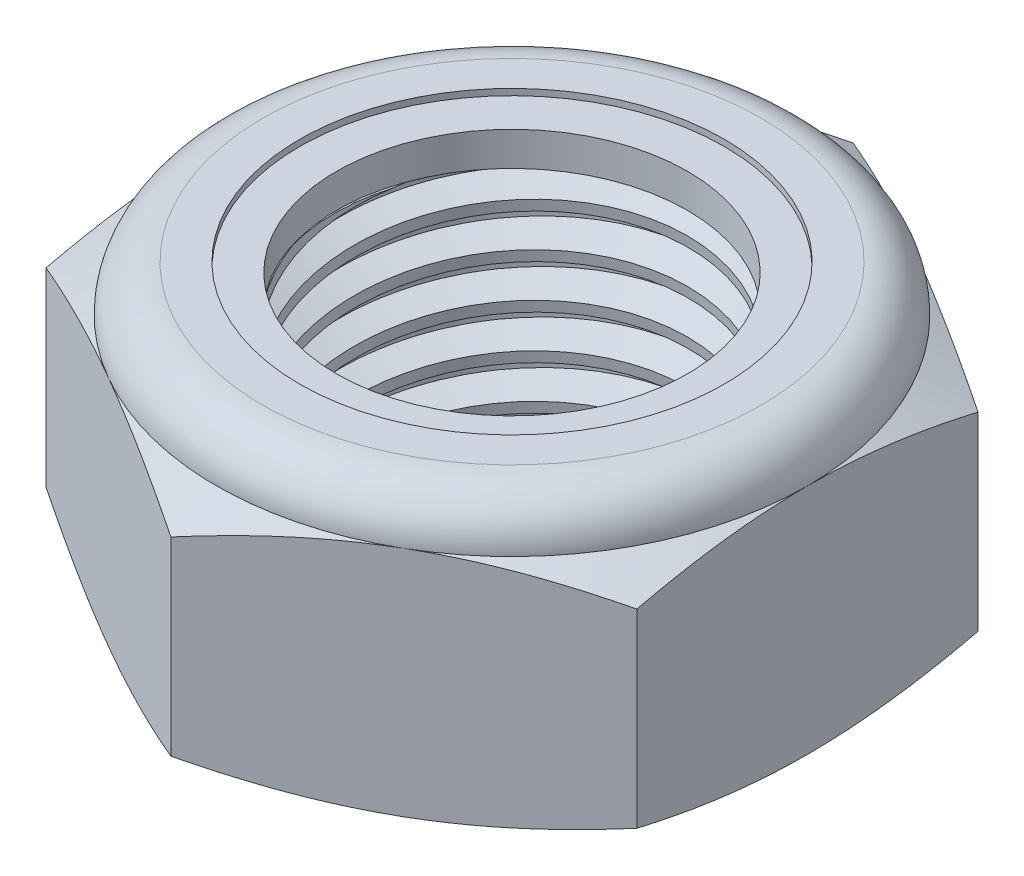
SolidWorks part; units mm, degrees
ref_plane "Front" through (0, 0, 0) normal (0, 0, 1) x (1, 0, 0)
ref_plane "Top" through (0, 0, 0) normal (0, 1, 0) x (1, 0, 0)
ref_plane "Right" through (0, 0, 0) normal (1, 0, 0) x (0, 0, -1)
sketch "Sketch1" plane through (0, 0, 0) normal (0, 1, 0) x (1, 0, 0)
  line L1 (0, 8.2489) -> (-7.1438, 4.1244)
  line L2 (-7.1438, 4.1244) -> (-7.1438, -4.1244)
  line L3 (-7.1438, -4.1244) -> (0, -8.2489)
  line L4 (0, -8.2489) -> (7.1437, -4.1244)
  line L5 (7.1437, -4.1244) -> (7.1437, 4.1244)
  line L6 (7.1437, 4.1244) -> (0, 8.2489)
  circle A0 centre (0, 0) radius 7.1438 construction
  dimension "Hex Flats" = 14.2875
extrude "Extrude1" add sketch "Sketch1" along normal blind 6.7469
sketch "Sketch2" plane through (0, 0, 0) normal (1, 0, 0) x (0, 0, -1)
  line L0 (-4.7625, 0) -> (-4.7625, 6.7469) construction
  line L1 (0, 0) -> (4.7625, 0)
  line L2 (0, 0) -> (0, 6.7469)
  line L3 (0, 6.7469) -> (4.7625, 6.7469)
  line L4 (4.7625, 0) -> (4.7625, 6.7469)
  line L5 (-4.1244, 6.7469) -> (4.1244, 6.7469) construction
  line L7 (0, -4.7625) -> (0, 0) construction
  dimension "Thread Dia" = 9.525
revolve "Revolve1" add sketch "Sketch2" angle 360 about L7
sketch "Sketch3" plane through (0, 0, 0) normal (1, 0, 0) x (0, 0, -1)
  line L0 (4.7625, 6.7469) -> (-4.7625, 6.7469) construction
  line L1 (-4.7625, 6.7469) -> (-4.7625, 5.6885) construction
  line L2 (-4.7625, 5.6885) -> (4.7625, 6.7469) construction
  line L3 (4.7625, 6.7469) -> (4.7771, 6.6154) construction
  line L4 (4.7771, 6.6154) -> (4.8794, 5.695)
  line L5 (4.8794, 5.695) -> (4.2735, 5.9605)
  line L6 (4.2735, 5.9605) -> (4.2443, 6.2234)
  line L7 (4.2443, 6.2234) -> (4.7771, 6.6154)
  line L8 (4.2589, 6.0919) -> (4.8282, 6.1552) construction
  line L9 (4.7625, 6.7469) -> (4.7625, 6.1479) construction
  line L10 (4.7625, 6.1479) -> (-4.7625, 5.0896) construction
  line L11 (-4.7625, 5.0896) -> (-4.7625, 5.6885) construction
  line L12 (-0.1253, 6.7469) -> (0.1253, 4.4906) construction
  line L13 (-4.7625, 0) -> (-4.7625, 6.7469) construction
  line L14 (0, 6.7469) -> (4.7625, 6.7469) construction
  line L15 (4.7625, 0) -> (4.7625, 6.7469) construction
  point P13 (0, 5.6187)
  dimension "D1" = 0.1323
  dimension "D2" = 0.2646
  dimension "Thread Pitch" = 1.0583
  dimension "D4" = 60
  dimension "D5" = 1.0583
revolve "Cut-Revolve1" cut sketch "Sketch3" angle 360 about L12
pattern_linear "LPattern1" count 6 spacing 1.0583 along (0, -1, 0) count 2 spacing 1.0583 along (0, 1, 0) of "Cut-Revolve1"
sketch "Sketch4" plane through (0, 0, 0) normal (1, 0, 0) x (0, 0, -1)
  line L0 (0, 6.7469) -> (4.7625, 6.7469)
  line L1 (4.7625, 6.7469) -> (4.2443, 6.5052)
  line L2 (4.2443, 6.5052) -> (4.2443, 0.2416)
  line L3 (4.2443, 0.2416) -> (4.7625, 0)
  line L4 (4.7625, 0) -> (0, 0)
  line L5 (0, 0) -> (0, 6.7469)
  line L6 (4.7625, 0) -> (4.7625, 6.7469) construction
  line L7 (0, 6.7469) -> (4.7625, 6.7469) construction
  line L8 (0, 0) -> (4.7625, 0) construction
  line L9 (0, 0) -> (0, 6.7469) construction
  line L10 (0, 6.7469) -> (0, 7.3186) construction
  dimension "D1" = 25
revolve "Cut-Revolve2" cut sketch "Sketch4" angle 360 about L10
combine bodies "Combine1" operation type subtract main body 112 bodies to subtract 111
sketch "Sketch5" plane through (0, 0, 0) normal (1, 0, 0) x (0, 0, -1)
  line L0 (0, 0) -> (7.1438, 0)
  line L1 (7.1438, 0) -> (8.2489, 0.5153)
  line L2 (8.2489, 0.5153) -> (8.2489, 5.1071)
  line L3 (8.2489, 5.1071) -> (7.1438, 5.6224)
  line L4 (6.0193, 6.7469) -> (6.0193, 8.0169)
  line L5 (6.0193, 8.0169) -> (9.5189, 8.0169)
  line L6 (9.5189, 8.0169) -> (9.5189, -1.27)
  line L7 (9.5189, -1.27) -> (0, -1.27)
  line L8 (0, -1.27) -> (0, 0)
  line L9 (7.1438, 5.6224) -> (7.1438, 0) construction
  line L10 (0, 0) -> (4.7625, 0) construction
  line L13 (8.2489, 2.8112) -> (9.5189, 2.8112) construction
  line L14 (8.2489, 6.7469) -> (8.2489, 0) construction
  line L15 (0, 0) -> (0, 8.0169) construction
  line L20 (0, 8.0169) -> (6.0193, 8.0169) construction
  line L22 (0, 6.7469) -> (4.7625, 6.7469) construction
  arc A0 (7.1438, 5.6224) -> (6.0193, 6.7469) centre (6.0193, 5.6224) ccw
  dimension "D1" = 25
  dimension "D2" = 1.27
  dimension "D3" = 6.7469
  dimension "D4" = 1.1245
revolve "Cut-Revolve3" cut sketch "Sketch5" angle 360 about L15
sketch "Sketch6" plane through (0, 0, 0) normal (1, 0, 0) x (0, 0, -1)
  line L0 (0, 5.6224) -> (6.9914, 5.6224)
  line L1 (6.0193, 6.5945) -> (5.1318, 6.5945)
  line L2 (0, 8.0169) -> (0, 5.6224)
  line L3 (5.1318, 8.0169) -> (0, 8.0169)
  line L4 (0, 8.0169) -> (6.0193, 8.0169) construction
  line L5 (0, 0) -> (0, 8.0169) construction
  line L6 (0, 8.0169) -> (0, 44.323) construction
  line L7 (5.1318, 6.5945) -> (5.1318, 8.0169)
  line L8 (6.0193, 6.7469) -> (6.0193, 6.5945) construction
  line L9 (5.1318, 6.5945) -> (4.2443, 6.5945) construction
  line L10 (4.2443, 6.5945) -> (4.2443, 6.5052) construction
  arc A0 (6.9914, 5.6224) -> (6.0193, 6.5945) centre (6.0193, 5.6224) ccw
  arc A1 (7.1438, 5.6224) -> (6.0193, 6.7469) centre (6.0193, 5.6224) ccw construction
  dimension "D1" = 0.1524
revolve "Cut-Revolve4" cut sketch "Sketch6" angle 360 about L6
sketch "Sketch7" plane through (0, 0, 0) normal (1, 0, 0) x (0, 0, -1)
  line L0 (4.2443, 5.6986) -> (6.9119, 5.6986)
  line L1 (6.0193, 6.5183) -> (4.2443, 6.5183)
  line L2 (4.2443, 6.5183) -> (4.2443, 5.6986)
  line L3 (4.2443, 5.6986) -> (0, 5.6986) construction
  line L4 (0, 5.6986) -> (0, 6.5183) construction
  line L5 (0, 6.5183) -> (4.2443, 6.5183) construction
  line L6 (4.2443, 5.6986) -> (4.2443, 5.6224) construction
  line L7 (0, 5.6224) -> (6.9914, 5.6224) construction
  line L8 (6.0193, 6.5183) -> (6.0193, 6.5945) construction
  arc A0 (6.9119, 5.6986) -> (6.0193, 6.5183) centre (6.0193, 5.6224) ccw
  arc A2 (6.9914, 5.6224) -> (6.0193, 6.5945) centre (6.0193, 5.6224) ccw construction
  dimension "D1" = 0.0762
revolve "Revolve2" add sketch "Sketch7" angle 360 about L4
equation "\"D1@Sketch3\"=\"Thread Pitch@Sketch3\"/8"
equation "\"D2@Sketch3\"=\"Thread Pitch@Sketch3\"/4"
equation "\"D5@Sketch3\"=\"Thread Pitch@Sketch3\""
equation "\"D4@LPattern1\"=\"Thread Pitch@Sketch3\""
equation "\"D3@LPattern1\"=\"Thread Pitch@Sketch3\""
equation "\"D1@LPattern1\"=\"Height@Extrude1\"/\"Thread Pitch@Sketch3\""
equation "\"D4@Sketch5\"=\"Height@Extrude1\"/6"
